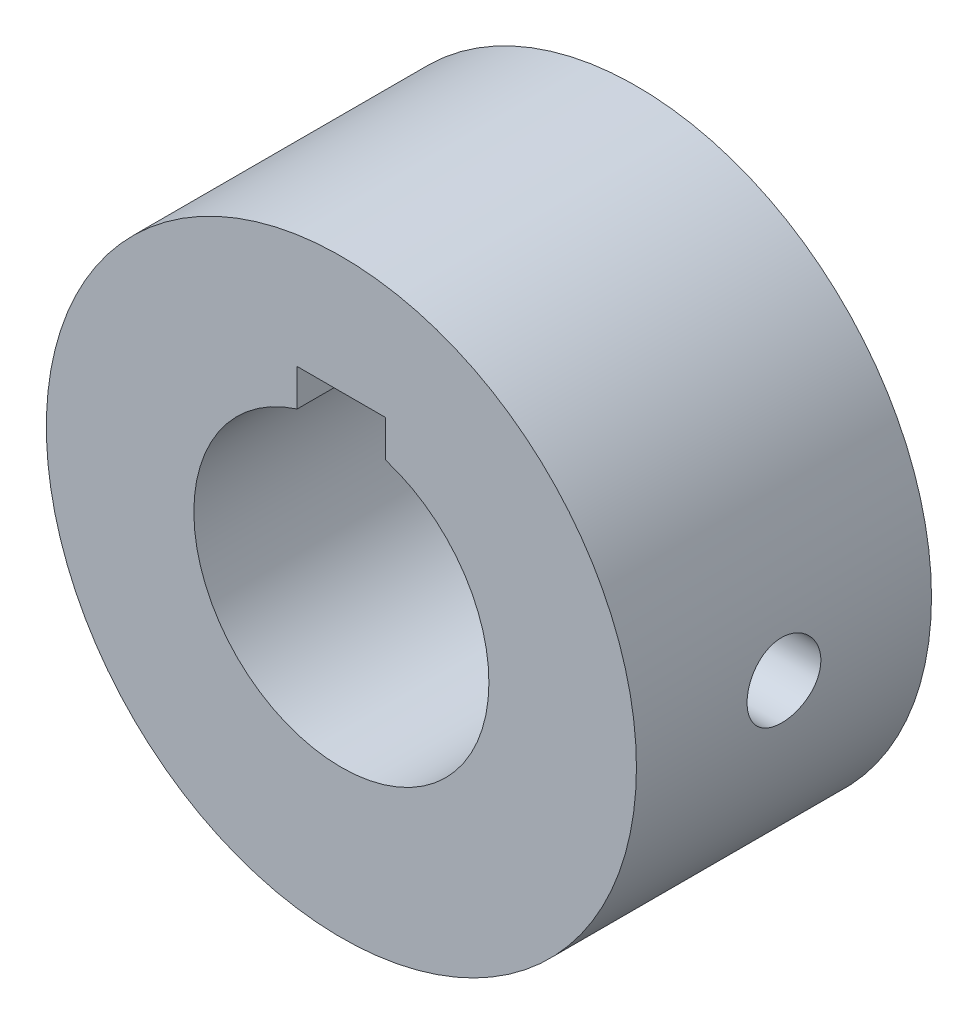
SolidWorks part; units mm, degrees
ref_plane "Plan de face" through (0, 0, 0) normal (0, 0, 1) x (1, 0, 0)
ref_plane "Plan de dessus" through (0, 0, 0) normal (0, 1, 0) x (1, 0, 0)
ref_plane "Plan de droite" through (0, 0, 0) normal (1, 0, 0) x (0, 0, -1)
sketch "Esquisse1" plane through (0, 0, 0) normal (0, 0, 1) x (1, 0, 0)
  circle A0 centre (0, 0) radius 20
  dimension "D1" = 40
extrude "Boss.-Extru.1" add sketch "Esquisse1" along normal blind 20
hole_wizard "Trou taraudé M61" positions "Esquisse3D1" profile "Esquisse10" tap size "M6" standard "ISO"
sketch3d "Esquisse3D1"
  point P1 (20, 0.0429, 10)
  dimension "D1" = 10
sketch "Esquisse10" plane through (20, 0.0429, 10) normal (0, 0, 1) x (-0.0021, 1, 0)
  line L0 (0, 0) -> (0, 18.5022)
  line L1 (0, 18.5022) -> (2.5, 17)
  line L2 (2.5, 17) -> (2.5, 0)
  line L5 (2.5, 0) -> (0, 0)
  line L10 (0, 18.5022) -> (-2.5, 17) construction
  line L11 (0, -6.35) -> (0, 107.95) construction
  dimension "Diamètre du trou pour taraudage" = 5
  dimension "Profondeur du trou pour taraudage" = 17
  dimension "Angle de pointe" = 118
cosmetic thread "Filetage de perçage1" parameters "D1"=10.3175, "D2"=6
sketch "Esquisse11" plane through (0, 0, 20) normal (0, 0, 1) x (1, 0, 0)
  line L2 (3, 9.5394) -> (3, 12.0394)
  line L3 (3, 12.0394) -> (-3, 12.0394)
  line L4 (-3, 9.5394) -> (-3, 12.0394)
  arc A0 (-3, 9.5394) -> (3, 9.5394) centre (0, 0) ccw
  dimension "D2" = 10
  dimension "D1" = 6
  dimension "D3" = 3
  dimension "D4" = 2.5
extrude "Enlèv. mat.-Extru.1" cut sketch "Esquisse11" against normal blind 25
